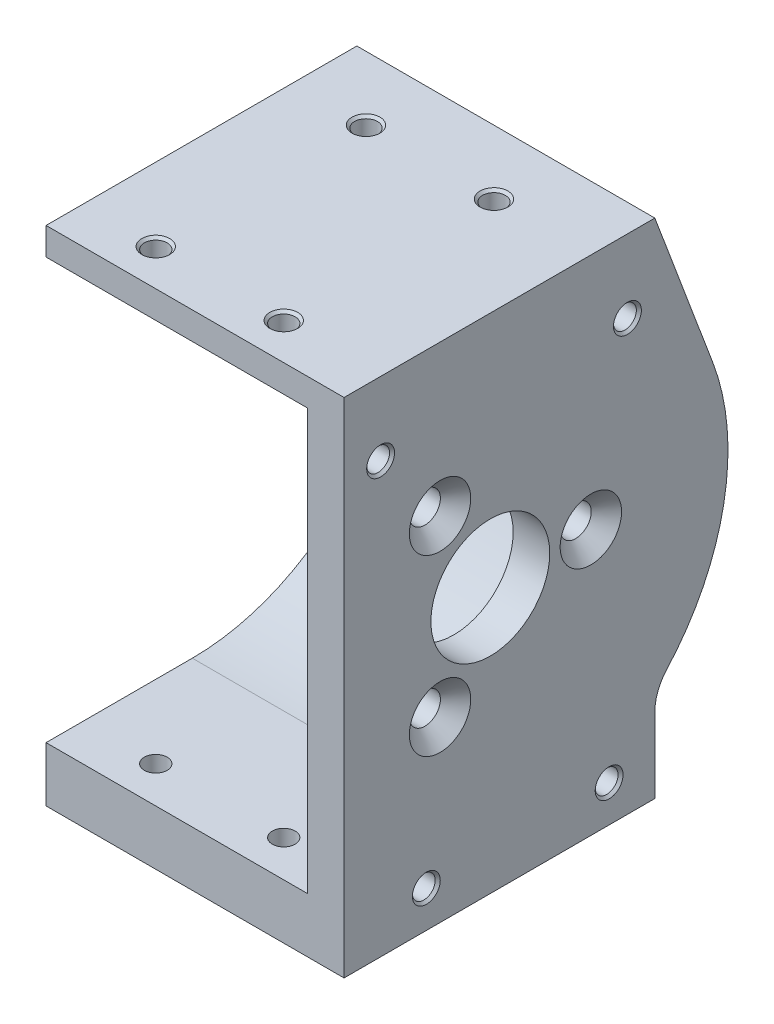
SolidWorks part; units mm, degrees
material "6061 Alloy"
ref_plane "Front Plane" through (0, 0, 0) normal (0, 0, 1) x (1, 0, 0)
ref_plane "Top Plane" through (0, 0, 0) normal (0, 1, 0) x (1, 0, 0)
ref_plane "Right Plane" through (0, 0, 0) normal (1, 0, 0) x (0, 0, -1)
ref_plane "Motor Face w/ 0.5mm tolerance" through (28.6, 0, 0) normal (1, 0, 0) x (0, 0, -1)
sketch "Motor Shell Profile" plane through (0, 0, 0) normal (1, 0, 0) x (0, 0, -1)
  line L0 (0, 22) -> (-16, 22)
  line L1 (-16, -29) -> (18, -29)
  line L2 (-16, 22) -> (-16, 26)
  line L3 (-16, 26) -> (18, 26)
  line L4 (18, -20.7846) -> (18, -29)
  line L5 (0, -22) -> (-16, -22)
  line L6 (-16, -22) -> (-16, -29)
  line L7 (24.336, 9.152) -> (18, 26)
  arc A0 (0, -22) -> (0, 22) centre (0, 0) ccw
  arc A1 (19.2903, -17.4323) -> (24.336, 9.152) centre (0, 0) ccw
  arc A2 (18, -20.7846) -> (19.2903, -17.4323) centre (23, -20.7846) cw
  point P17 (18, -29)
  dimension "D1" = 4
  dimension "Motor Diameter" = 22
  dimension "D3" = 26
  dimension "D6" = 5
  dimension "D2" = 7
  dimension "D4" = 16
  dimension "D5" = 34
extrude "Motor Shell" add sketch "Motor Shell Profile" along normal offset from surface (32.6 mm away) 4 up to plane "Motor Face w/ 0.5mm tolerance" offset beyond the face yes
sketch "Sketch3" plane through (28.6, 0, 0) normal (1, 0, 0) x (0, 0, -1)
  line L0 (0, 22) -> (-16, 22)
  line L1 (-16, -22) -> (0, -22)
  line L2 (-16, 22) -> (-16, -22)
  arc A0 (0, 22) -> (0, -22) centre (0, 0) cw
  circle A2 centre (0, 0) radius 11 construction
  arc A3 (0, -22) -> (0, 22) centre (0, 0) ccw construction
  dimension "D1" = 22
extrude "Motor Mount" add sketch "Sketch3" along normal blind 4
hole_wizard "Mounting Hole" positions "Sketch9" profile "Sketch10" countersink size "M3" standard "ANSI Metric" end condition through all
sketch "Sketch9" plane through (32.6, 0, 0) normal (1, 0, 0) x (0, 0, -1)
  point P0 (11, 0)
  dimension "D1" = 11
sketch "Sketch10" plane through (32.6, 0, -11) normal (0, 1, 0) x (0, 0, -1)
  line L0 (0, 0) -> (0, 32.6)
  line L1 (0, 32.6) -> (1.7, 32.6)
  line L2 (1.7, 32.6) -> (1.7, 1.66)
  line L3 (1.7, 1.66) -> (3.36, 0)
  line L5 (3.36, 0) -> (0, 0)
  line L6 (-1.7, 1.66) -> (-3.36, 0) construction
  line L11 (0, -6.35) -> (0, 107.95) construction
  dimension "Thru Hole Dia." = 3.4
  dimension "Thru Hole Depth" = 32.6
  dimension "Near C'Sink Dia." = 6.72
  dimension "Near C'Sink Angle" = 90
pattern_circular "Hole Duplication" count 3 over 360 about axis through (0, 0, 0) along (1, 0, 0) of "Mounting Hole"
sketch "Sketch11" plane through (32.6, 0, 0) normal (1, 0, 0) x (0, 0, -1)
  circle A0 centre (0, 0) radius 6.5
  dimension "D1" = 13
extrude "Shaft Base Cutout" cut sketch "Sketch11" against normal through all
ref_plane "U Joint Base Plane" through (35.1, 0, 0) normal (1, 0, 0) x (0, 0, -1)
ref_plane "Pin Hole Plane" through (0, 0, 15) normal (0, 0, 1) x (1, 0, 0)
hole_wizard "M3x0.5 Tapped Hole1" positions "Sketch13" profile "Sketch15" tap size "M3x0.5" standard "ANSI Metric"
sketch "Sketch13" plane through (32.6, 0, 0) normal (1, 0, 0) x (0, 0, -1)
  point P0 (-7, -25)
  point P2 (13, -25)
  point P9 (-12, 18)
  point P11 (15, 18)
  dimension "D1" = 20
  dimension "D2" = 25
  dimension "D3" = 7
  dimension "D4" = 18
  dimension "D5" = 27
  dimension "D6" = 15
sketch "Sketch15" plane through (32.6, -25, 7) normal (0, 1, 0) x (0, 0, -1)
  line L0 (0, 0) -> (0, 5.7511)
  line L1 (0, 5.7511) -> (1.25, 5)
  line L2 (1.25, 5) -> (1.25, 0.275)
  line L3 (1.25, 0.275) -> (1.525, 0)
  line L5 (1.525, 0) -> (0, 0)
  line L6 (-1.25, 0.275) -> (-1.525, 0) construction
  line L10 (0, 5.7511) -> (-1.25, 5) construction
  line L11 (0, -6.35) -> (0, 107.95) construction
  dimension "Tap Drill Dia." = 2.5
  dimension "Tap Drill Depth" = 5
  dimension "Near C'Sink Dia." = 3.05
  dimension "Near C'Sink Angle" = 90
  dimension "Drill Angle" = 118
sketch "Sketch16" plane through (32.6, 0, 0) normal (1, 0, 0) x (0, 0, -1)
  line L0 (-16, -29) -> (-16, -13)
  line L1 (-16, -29) -> (18, -29) construction
  line L2 (-16, -13) -> (22.5167, -13)
  line L3 (22.5167, -13) -> (22.5167, -29)
  line L4 (22.5167, -29) -> (-16, -29)
  line L5 (18, -29) -> (18, -20.7846) construction
  arc A0 (19.2903, -17.4323) -> (24.336, 9.152) centre (0, 0) ccw construction
  point P14 (18, -24.8923)
  dimension "D1" = 16
  dimension "D2" = 34
extrude "Pin Mount Recess" [suppressed] cut sketch "Sketch16" against normal blind 2
hole_wizard "M3x0.5 Tapped Hole2" positions "Sketch17" profile "Sketch18" tap size "M3x0.5" standard "ANSI Metric" end condition through all
sketch "Sketch17" plane through (0, 26, 0) normal (0, 1, 0) x (1, 0, 0)
  line L2 (0, 1) -> (38.3988, 1) construction
  line L3 (0, 18) -> (0, -16) construction
  point P0 (22, -12)
  point P2 (8, -12)
  point P17 (8, 11)
  point P19 (22, 11)
  dimension "D1" = 13
  dimension "D2" = 14
  dimension "D3" = 8
  dimension "D4" = 10
sketch "Sketch18" plane through (22, 26, 12) normal (1, 0, 0) x (0, 0, 1)
  line L0 (0, 0) -> (0, 55)
  line L1 (0, 55) -> (1.25, 55)
  line L2 (1.25, 55) -> (1.25, 0.275)
  line L3 (1.25, 0.275) -> (1.525, 0)
  line L5 (1.525, 0) -> (0, 0)
  line L6 (-1.25, 0.275) -> (-1.525, 0) construction
  line L11 (0, -6.35) -> (0, 107.95) construction
  dimension "Thru Tap Drill Dia." = 2.5
  dimension "Thru Tap Drill Depth" = 55
  dimension "Near C'Sink Dia." = 3.05
  dimension "Near C'Sink Angle" = 90
hole_wizard "M3x0.5 Tapped Hole3" positions "Sketch21" profile "Sketch22" tap size "M3x0.5" standard "ANSI Metric"
sketch "Sketch21" plane through (0, 0, -18) normal (0, 0, -1) x (-1, 0, 0)
  line L0 (-32.6, -29) -> (0, -29) construction
  line L1 (0, -29) -> (0, -20.7846) construction
  point P0 (-24, -24.2)
  dimension "D1" = 4.8
  dimension "D2" = 24
sketch "Sketch22" plane through (24, -24.2, -18) normal (1, 0, 0) x (0, 1, 0)
  line L0 (0, 0) -> (0, 5.7511)
  line L1 (0, 5.7511) -> (1.25, 5)
  line L2 (1.25, 5) -> (1.25, 0)
  line L5 (1.25, 0) -> (0, 0)
  line L10 (0, 5.7511) -> (-1.25, 5) construction
  line L11 (0, -6.35) -> (0, 107.95) construction
  dimension "Tap Drill Dia." = 2.5
  dimension "Tap Drill Depth" = 5
  dimension "Drill Angle" = 118
cosmetic thread "Hole Thread5" parameters "D1"=5, "D2"=3
ref_plane "Plane1" through (0, 0, -25) normal (0, 0, 1) x (1, 0, 0)
hole_wizard "Tap Drill for M3x0.5 Tap2" positions "Sketch23" profile "Sketch24" hole size "M3x0.5" standard "ANSI Metric"
sketch "Sketch23" plane through (0, 0, -25) normal (0, 0, 1) x (1, 0, 0)
  line L0 (0, 9.152) -> (0, 26) construction
  line L1 (32.6, 26) -> (0, 26) construction
  point P0 (14, 21.5)
  dimension "D1" = 14
  dimension "D2" = 4.5
sketch "Sketch24" plane through (14, 21.5, -25) normal (1, 0, 0) x (0, 1, 0)
  line L0 (0, 0) -> (0, 15.7511)
  line L1 (0, 15.7511) -> (1.25, 15)
  line L2 (1.25, 15) -> (1.25, 0)
  line L5 (1.25, 0) -> (0, 0)
  line L10 (0, 15.7511) -> (-1.25, 15) construction
  line L11 (0, -6.35) -> (0, 107.95) construction
  dimension "Hole Dia." = 2.5
  dimension "Hole Depth" = 15
  dimension "Drill Angle" = 118
sketch "Sketch25" plane through (0, 0, 0) normal (-1, 0, 0) x (0, 0, 1)
  line L0 (0, 23) -> (16, 23)
  line L1 (16, 26) -> (16, 22) construction
  line L2 (0, -23) -> (16, -23)
  line L3 (16, -22) -> (16, -29) construction
  line L4 (16, -23) -> (16, 23)
  arc A0 (0, 23) -> (0, -23) centre (0, 0) ccw
  dimension "D1" = 46
extrude "Cut-Extrude1" cut sketch "Sketch25" against normal up to surface (28.6 mm away) up to face at (28.6, 18, 13.25)
